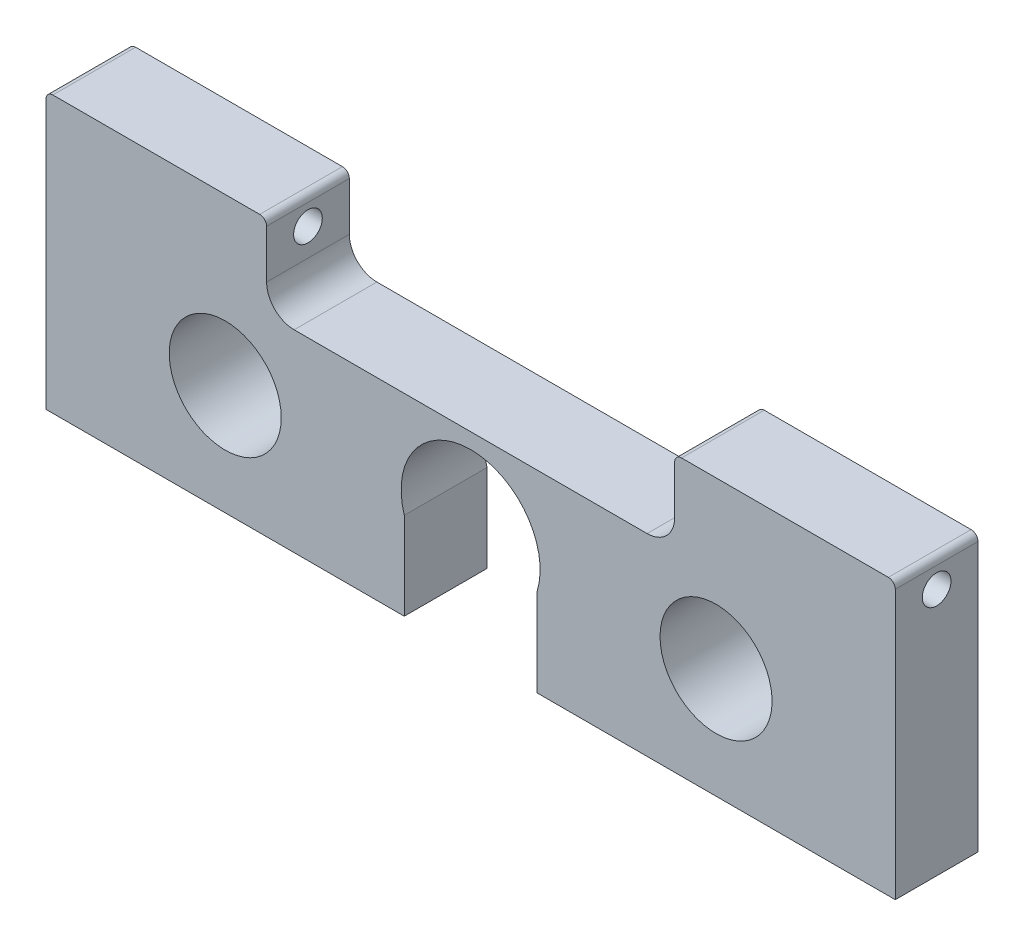
SolidWorks part; units mm, degrees
ref_plane "Front Plane" through (0, 0, 0) normal (0, 0, 1) x (1, 0, 0)
ref_plane "Top Plane" through (0, 0, 0) normal (0, 1, 0) x (1, 0, 0)
ref_plane "Right Plane" through (0, 0, 0) normal (1, 0, 0) x (0, 0, -1)
sketch "Sketch1" plane through (0, 0, 0) normal (0, 0, 1) x (1, 0, 0)
  line L1 (-97.79, -19.05) -> (97.79, -19.05)
  line L2 (-97.79, -19.05) -> (-97.79, 19.05)
  line L3 (-97.79, 19.05) -> (97.79, 19.05)
  line L4 (97.79, -19.05) -> (97.79, 19.05)
  line L5 (-97.79, -19.05) -> (97.79, 19.05) construction
  line L6 (-97.79, 19.05) -> (97.79, -19.05) construction
  point P0 (0, 0)
  dimension "D1" = 38.1
  dimension "D2" = 195.58
extrude "Boss-Extrude1" add sketch "Sketch1" along normal blind 19.05
sketch "Sketch2" plane through (0, 0, 19.05) normal (0, 0, 1) x (1, 0, 0)
  line L0 (0, 75.2361) -> (0, -75.2361) construction
  line L1 (-97.79, 19.05) -> (-97.79, -19.05) construction
  circle A0 centre (-56.515, 0) radius 12.8984
  circle A1 centre (56.515, 0) radius 12.8984
  point P4 (0, 0)
  dimension "D1" = 25.7969
  dimension "D2" = 41.275
extrude "Cut-Extrude1" cut sketch "Sketch2" against normal through all
sketch "Sketch3" plane through (0, 0, 19.05) normal (0, 0, 1) x (1, 0, 0)
  line L0 (-14.5542, -5.0283) -> (-9.525, -21.2064) construction
  line L1 (-9.525, -21.2064) -> (9.525, -21.2064) construction
  line L2 (9.525, -21.2064) -> (14.5542, -5.0283) construction
  line L3 (-15.2819, -5.2544) -> (-10.0861, -21.9684)
  line L4 (-10.0861, -21.9684) -> (10.0861, -21.9684)
  line L5 (10.0861, -21.9684) -> (15.2819, -5.2544)
  arc A0 (14.5542, -5.0283) -> (-14.5542, -5.0283) centre (0, -0.508) ccw construction
  arc A1 (15.2819, -5.2544) -> (-15.2819, -5.2544) centre (0, -0.508) ccw
  arc A2 (14.5542, -5.0283) -> (-14.5542, -5.0283) centre (0, -0.508) ccw construction
  point P21 (0, -21.2064)
  dimension "D1" = 30.48
  dimension "D2" = 16.9418
  dimension "D3" = 19.05
  dimension "D4" = 5.0292
  dimension "D6" = 0.508
  dimension "D5" = 0.762
extrude "Cut-Extrude2" cut sketch "Sketch3" against normal through all contours L2 A0 L0 L1 | L5 A1 L3 L4 A0 L2 L1 L0
sketch "Sketch4" plane through (-97.79, 0, 0) normal (-1, 0, 0) x (0, 0, 1)
  line L6 (0, 19.05) -> (19.05, 19.05)
  line L7 (0, 19.05) -> (0, 38.1)
  line L8 (0, 38.1) -> (19.05, 38.1)
  line L9 (19.05, 19.05) -> (19.05, 38.1)
  dimension "D1" = 19.05
extrude "Boss-Extrude2" add sketch "Sketch4" against normal blind 50.8
sketch "Sketch6" plane through (-97.79, 0, 0) normal (-1, 0, 0) x (0, 0, 1)
  line L0 (19.05, 19.05) -> (0, 19.05) construction
  line L2 (19.05, 38.1) -> (0, 38.1) construction
  circle A0 centre (9.525, 31.75) radius 3.302
  point P4 (9.525, 19.05)
  dimension "D1" = 6.604
  dimension "D2" = 6.35
extrude "Cut-Extrude3" cut sketch "Sketch6" against normal through all
mirror "Mirror2" about plane through (0, 0, 0) normal (1, 0, 0) of "Cut-Extrude3", "Boss-Extrude2"
fillet "Fillet1" radius 6.35 2 edges at (46.99, 19.05, 9.525) (-46.99, 19.05, 9.525)
fillet "Fillet2" radius 1.5875 4 edges at (46.99, 38.1, 9.525) (97.79, 38.1, 9.525) (-46.99, 38.1, 9.525) (-97.79, 38.1, 9.525)
sketch "Sketch7" plane through (0, 0, 19.05) normal (0, 0, 1) x (1, 0, 0)
  line L0 (-97.79, -19.05) -> (-97.79, -25.4)
  line L1 (-97.79, -25.4) -> (-10.9933, -25.4)
  line L2 (97.79, -25.4) -> (97.79, -19.05)
  line L3 (97.79, -19.05) -> (97.79, 36.5125) construction
  line L4 (10.9933, -19.05) -> (97.79, -19.05) construction
  line L10 (-97.79, -19.05) -> (-10.9933, -19.05)
  line L11 (10.9933, -19.05) -> (97.79, -19.05)
  line L12 (10.9933, -19.05) -> (10.9933, -25.4)
  line L13 (-10.9933, -19.05) -> (-10.9933, -25.4)
  line L14 (10.9933, -25.4) -> (97.79, -25.4)
  dimension "D1" = 6.35
extrude "Boss-Extrude3" add sketch "Sketch7" against normal up to surface (19.05 mm away) up to face at (0, 17.7819, 0)
sketch "Sketch8" plane through (0, 0, 19.05) normal (0, 0, 1) x (1, 0, 0)
  line L0 (-15.2819, -5.2544) -> (-15.2819, -25.4)
  line L1 (-97.79, -25.4) -> (-10.9933, -25.4) construction
  line L2 (15.2819, -5.2544) -> (15.2819, -25.4)
  line L3 (10.9933, -25.4) -> (97.79, -25.4) construction
  line L4 (-15.2819, -5.2544) -> (15.2819, -5.2544)
  line L5 (15.2819, -25.4) -> (-15.2819, -25.4)
extrude "Cut-Extrude4" cut sketch "Sketch8" against normal through all and the other way through all
